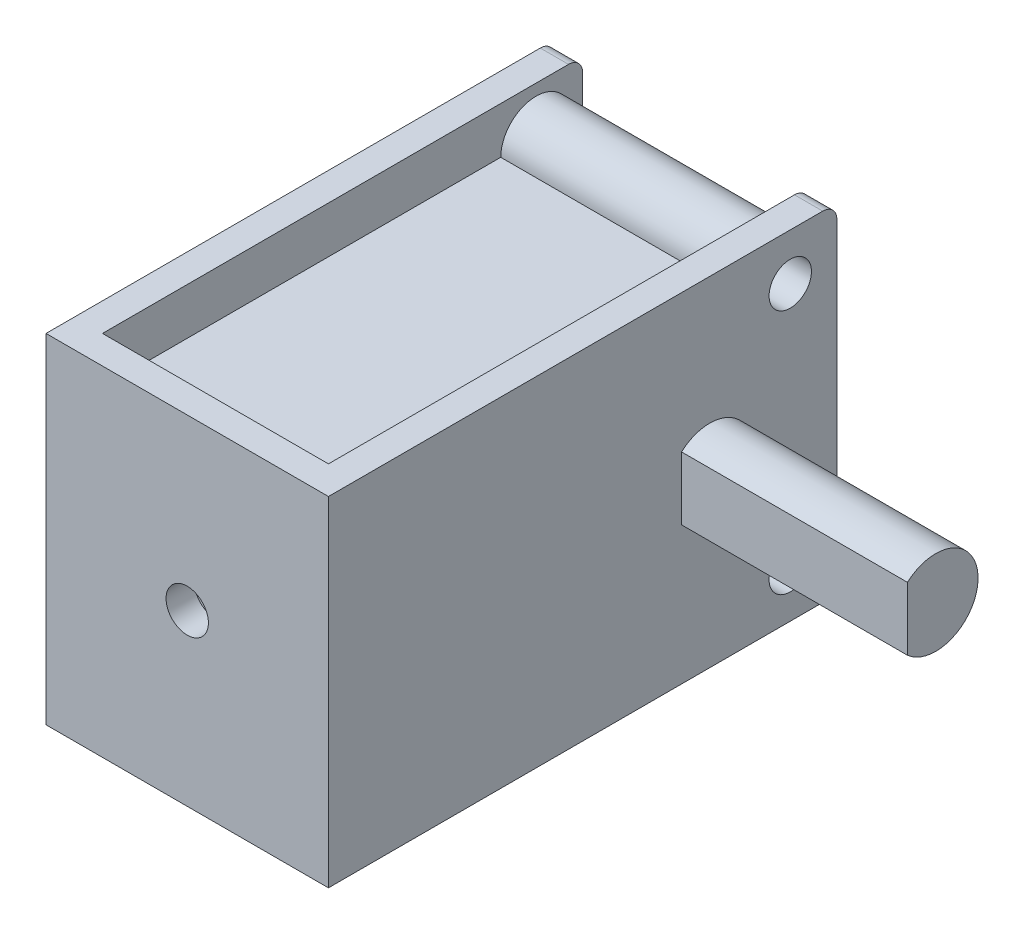
SolidWorks part; units mm, degrees
ref_plane "Plano frontal" through (0, 0, 0) normal (0, 0, 1) x (1, 0, 0)
ref_plane "Plano superior" through (0, 0, 0) normal (0, 1, 0) x (1, 0, 0)
ref_plane "Plano direito" through (0, 0, 0) normal (1, 0, 0) x (0, 0, -1)
sketch "Esboço1" plane through (0, 0, 0) normal (0, 1, 0) x (1, 0, 0)
  line L1 (-5, -9) -> (5, -9)
  line L2 (-5, -9) -> (-5, 9)
  line L3 (-5, 9) -> (5, 9)
  line L4 (5, -9) -> (5, 9)
  line L5 (-5, -9) -> (5, 9) construction
  line L6 (-5, 9) -> (5, -9) construction
  point P0 (0, 0)
  dimension "D1" = 18
  dimension "D2" = 10
extrude "Ressalto-extrusão1" add sketch "Esboço1" along normal mid plane 12
sketch "Esboço2" plane through (5, 0, 0) normal (1, 0, 0) x (0, 0, -1)
  line L0 (9, 6) -> (9, -6) construction
  line L1 (3.5, 1.118) -> (3.5, -1.118)
  arc A0 (3.5, -1.118) -> (3.5, 1.118) centre (4.5, 0) ccw
  dimension "D1" = 3
  dimension "D2" = 4.5
  dimension "D3" = 1
extrude "Ressalto-extrusão2" add sketch "Esboço2" along normal blind 8
fillet "Filete1" radius 0.5 2 edges at (0, -6, -9) (0, 6, -9)
sketch "Esboço3" plane through (0, 6, 0) normal (0, 1, 0) x (1, 0, 0)
  line L8 (-4, 9) -> (-4, -8)
  line L9 (-5, 9) -> (5, 9) construction
  line L10 (-4, -8) -> (4, -8)
  line L11 (4, -8) -> (4, 9)
  line L12 (-5, -9) -> (5, -9) construction
  line L13 (-4, 9) -> (4, 9)
  point P8 (0, -8)
  dimension "D2" = 8
  dimension "D1" = 1
extrude "Corte-extrusão1" cut sketch "Esboço3" against normal through all
sketch "Esboço4" plane through (5, 0, 0) normal (1, 0, 0) x (0, 0, -1)
  line L0 (9, 5.5) -> (9, -5.5) construction
  line L1 (-9, 6) -> (8.5, 6) construction
  line L2 (9.9, 0) -> (-9.9, 0) construction
  circle A0 centre (7.35, 4.35) radius 1.25
  circle A1 centre (7.35, -4.35) radius 1.25
  dimension "D3" = 2.5
  dimension "D1" = 1.65
  dimension "D2" = 1.65
extrude "Ressalto-extrusão3" add sketch "Esboço4" against normal through all
sketch "Esboço5" plane through (5, 0, 0) normal (1, 0, 0) x (0, 0, -1)
  line L0 (9.9, 0) -> (-9.9, 0) construction
  circle A0 centre (7.35, 4.35) radius 1.25 construction
  circle A1 centre (7.35, 4.35) radius 1.25 construction
  circle A3 centre (7.35, 4.35) radius 0.75
  circle A4 centre (7.35, -4.35) radius 0.75
  dimension "D1" = 0.5
extrude "Corte-extrusão2" cut sketch "Esboço5" against normal through all
sketch "Esboço6" plane through (0, 0, 9) normal (0, 0, 1) x (1, 0, 0)
  circle A0 centre (0, 0) radius 0.75
  dimension "D1" = 1.5
extrude "Corte-extrusão3" cut sketch "Esboço6" against normal up to next
sketch "Esboço7" plane through (-4, 0, 0) normal (1, 0, 0) x (0, 0, -1)
  line L0 (-8, -6) -> (-8, 6) construction
  line L1 (-8, 4.35) -> (6.6, 4.35)
  line L2 (-8, 4.35) -> (-8, -4.35)
  line L3 (-8, -4.35) -> (6.6, -4.35)
  line L4 (6.6, 4.35) -> (6.6, -4.35)
  circle A1 centre (7.35, -4.35) radius 0.75 construction
  point P8 (6.6, 0)
  point P9 (0, 0)
extrude "Ressalto-extrusão6" add sketch "Esboço7" along normal up to next
